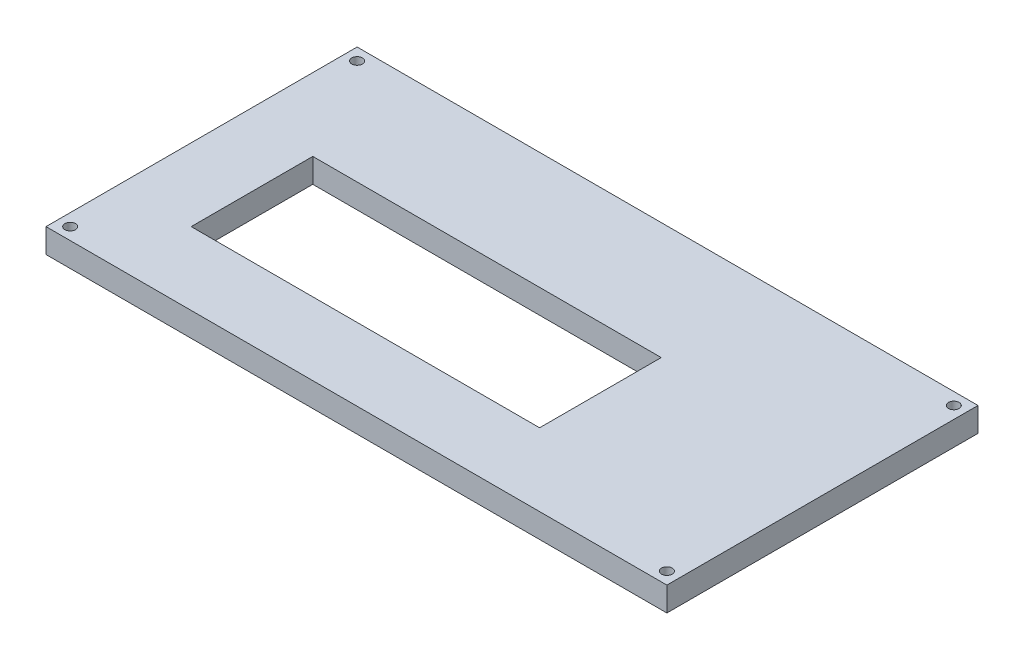
SolidWorks part; units mm, degrees
ref_plane "Front Plane" through (0, 0, 0) normal (0, 0, 1) x (1, 0, 0)
ref_plane "Top Plane" through (0, 0, 0) normal (0, 1, 0) x (1, 0, 0)
ref_plane "Right Plane" through (0, 0, 0) normal (1, 0, 0) x (0, 0, -1)
sketch "Sketch1" plane through (0, 0, 0) normal (0, 1, 0) x (1, 0, 0)
  line L0 (0, 0) -> (-128.3, 0)
  line L1 (-128.3, 0) -> (-128.3, 64.29)
  line L2 (-128.3, 64.29) -> (0, 64.29)
  line L3 (0, 64.29) -> (0, 0)
  dimension "D1" = 128.3
  dimension "D2" = 64.29
extrude "Boss-Extrude1" add sketch "Sketch1" along normal blind 5
sketch "Sketch2" plane through (0, 0, 0) normal (0, -1, 0) x (-1, 0, 0)
  line L0 (125.8, 2.5) -> (125.8, 61.79) construction
  line L1 (125.8, 61.79) -> (2.5, 61.79) construction
  line L2 (2.5, 61.79) -> (2.5, 2.5) construction
  line L3 (2.5, 2.5) -> (125.8, 2.5) construction
  line L4 (125.8, 2.5) -> (125.8, 0) construction
  line L5 (128.3, 0) -> (0, 0) construction
  line L6 (125.8, 2.5) -> (128.3, 2.5) construction
  line L7 (128.3, 64.29) -> (128.3, 0) construction
  line L8 (125.8, 61.79) -> (125.8, 64.29) construction
  line L9 (0, 64.29) -> (128.3, 64.29) construction
  line L10 (2.5, 2.5) -> (0, 2.5) construction
  line L11 (0, 0) -> (0, 64.29) construction
  circle A0 centre (125.8, 2.5) radius 1.1
  circle A1 centre (125.8, 61.79) radius 1.1
  circle A2 centre (2.5, 2.5) radius 1.1
  circle A3 centre (2.5, 61.79) radius 1.1
  dimension "D1" = 2.2
  dimension "D2" = 2.5
  dimension "D3" = 2.5
extrude "Cut-Extrude1" cut sketch "Sketch2" against normal through all
sketch "Sketch3" plane through (0, 0, 0) normal (0, -1, 0) x (1, 0, 0)
  line L0 (-113.3, -15) -> (-113.3, -40.13)
  line L1 (-113.3, -40.13) -> (-41.3, -40.13)
  line L2 (-41.3, -40.13) -> (-41.3, -15)
  line L3 (-41.3, -15) -> (-113.3, -15)
  line L4 (-113.3, -15) -> (-128.3, -15) construction
  line L5 (-128.3, -64.29) -> (-128.3, 0) construction
  line L6 (-113.3, -15) -> (-113.3, 0) construction
  line L7 (-128.3, 0) -> (0, 0) construction
  dimension "D1" = 15
  dimension "D2" = 15
  dimension "D3" = 25.13
  dimension "D4" = 72
extrude "Cut-Extrude2" cut sketch "Sketch3" against normal through all
